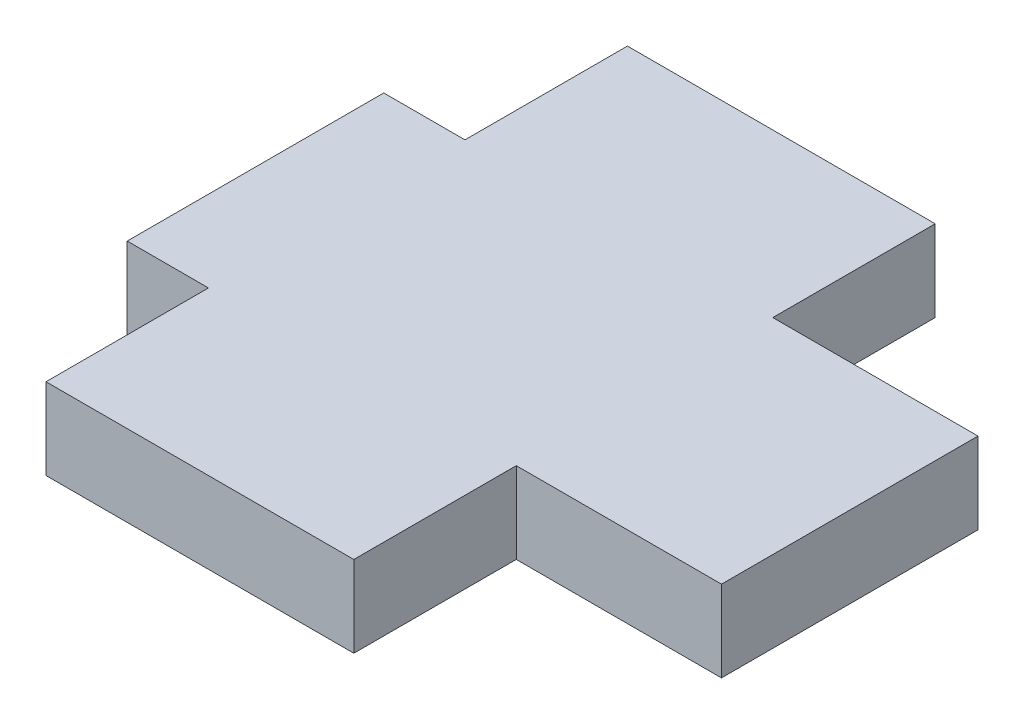
SolidWorks part; units mm, degrees
ref_plane "Front" through (0, 0, 0) normal (0, 0, 1) x (1, 0, 0)
ref_plane "Top" through (0, 0, 0) normal (0, 1, 0) x (1, 0, 0)
ref_plane "Right" through (0, 0, 0) normal (1, 0, 0) x (0, 0, -1)
sketch "Sketch1" plane through (0, 0, 0) normal (0, 1, 0) x (1, 0, 0)
  line L0 (11.43, 43.18) -> (11.43, 0) construction
  line L1 (0, 0) -> (22.86, 0)
  line L2 (0, 0) -> (0, 12.065)
  line L3 (0, 43.18) -> (22.86, 43.18)
  line L4 (22.86, 0) -> (22.86, 12.065)
  line L5 (0, 12.065) -> (-6.0325, 12.065)
  line L7 (0, 31.115) -> (-6.0325, 31.115)
  line L8 (-6.0325, 12.065) -> (-6.0325, 31.115)
  line L9 (0, 31.115) -> (0, 43.18)
  line L10 (22.86, 31.115) -> (22.86, 43.18)
  line L11 (22.86, 12.065) -> (38.1, 12.065)
  line L13 (22.86, 31.115) -> (38.1, 31.115)
  line L14 (38.1, 12.065) -> (38.1, 31.115)
  point P11 (-6.0325, 21.59)
  point P12 (11.43, 21.59)
  dimension "D1" = 22.86
  dimension "D2" = 43.18
  dimension "D3" = 19.05
  dimension "D4" = 6.0325
  dimension "D5" = 15.24
extrude "Boss-Extrude1" add sketch "Sketch1" along normal blind 6.0325
